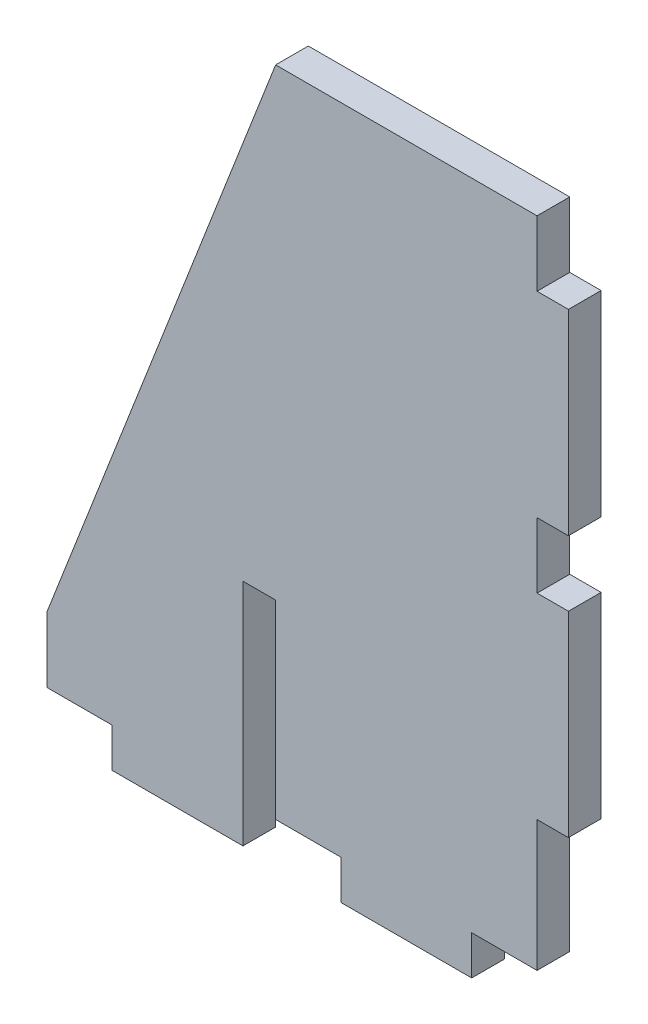
SolidWorks part; units mm, degrees
ref_plane "Front Plane" through (0, 0, 0) normal (0, 0, 1) x (1, 0, 0)
ref_plane "Top Plane" through (0, 0, 0) normal (0, 1, 0) x (1, 0, 0)
ref_plane "Right Plane" through (0, 0, 0) normal (1, 0, 0) x (0, 0, -1)
sketch "Sketch1" plane through (0, 0, 0) normal (0, 0, 1) x (1, 0, 0)
  line L1 (0, 0) -> (-6.35, 0)
  line L2 (0, 0) -> (0, 12.7)
  line L3 (0, 63.5) -> (-25.4, 63.5)
  line L6 (-28.575, 0) -> (-28.575, 18.4658)
  line L14 (-19.05, 0) -> (-19.05, -3.81)
  line L15 (-19.05, -3.81) -> (-6.35, -3.81)
  line L16 (-6.35, -3.81) -> (-6.35, 0)
  line L19 (-47.625, 0) -> (-47.625, 6.35)
  line L20 (-47.625, 6.35) -> (-25.4, 63.5)
  line L21 (0, 57.15) -> (3.048, 57.15)
  line L22 (3.048, 57.15) -> (3.048, 38.1)
  line L23 (3.048, 38.1) -> (0, 38.1)
  line L24 (0, 31.75) -> (3.048, 31.75)
  line L25 (3.048, 31.75) -> (3.048, 12.7)
  line L26 (3.048, 12.7) -> (0, 12.7)
  line L27 (0, 57.15) -> (0, 63.5)
  line L28 (0, 31.75) -> (0, 38.1)
  line L30 (-19.05, 0) -> (-25.4, 0)
  line L31 (-25.4, 0) -> (-25.4, 18.4658)
  line L32 (-25.4, 18.4658) -> (-28.575, 18.4658)
  line L33 (-28.575, 0) -> (-28.575, -3.81)
  line L34 (-28.575, -3.81) -> (-41.275, -3.81)
  line L35 (-41.275, -3.81) -> (-41.275, 0)
  line L36 (-41.275, 0) -> (-47.625, 0)
  dimension "D1" = 63.5
  dimension "D2" = 3.81
  dimension "D3" = 12.7
  dimension "D4" = 6.35
  dimension "D5" = 3.175
  dimension "D6" = 12.7
  dimension "D7" = 6.35
  dimension "D8" = 25.4
  dimension "D9" = 22.2758
  dimension "D10" = 3.048
  dimension "D11" = 6.35
  dimension "D12" = 6.35
  dimension "D13" = 3.048
  dimension "D14" = 19.05
  dimension "D15" = 19.05
  dimension "D16" = 12.7
  dimension "D17" = 38.1
extrude "Boss-Extrude1" add sketch "Sketch1" along normal blind 3.175 contours L14 L15 L16 L1 L2 L26 L25 L24 L28 L23 L22 L21 L27 L3 L20 L19 L36 L35 L34 L33 L6 L32 L31 L30
sketch "Sketch2" plane through (0, 0, 3.175) normal (0, 0, 1) x (1, 0, 0)
  line L32 (-25.4, 0) -> (-19.05, 0)
  line L33 (-19.05, 0) -> (-19.05, -3.81)
  line L34 (-19.05, -3.81) -> (-6.35, -3.81)
  line L35 (-6.35, -3.81) -> (-6.35, 0)
  line L36 (-6.35, 0) -> (0, 0)
  line L37 (0, 0) -> (0, 12.7)
  line L38 (0, 12.7) -> (3.048, 12.7)
  line L39 (3.048, 12.7) -> (3.048, 31.75)
  line L40 (3.048, 31.75) -> (0, 31.75)
  line L41 (0, 31.75) -> (0, 38.1)
  line L42 (0, 38.1) -> (3.048, 38.1)
  line L43 (3.048, 38.1) -> (3.048, 57.15)
  line L44 (3.048, 57.15) -> (0, 57.15)
  line L45 (0, 57.15) -> (0, 63.5)
  line L46 (0, 63.5) -> (-25.4, 63.5)
  line L47 (-25.4, 63.5) -> (-47.625, 6.35)
  line L48 (-47.625, 6.35) -> (-47.625, 0)
  line L49 (-25.4, 0) -> (-19.05, 0)
  line L54 (-28.575, -3.81) -> (-28.575, 18.4658)
  line L56 (-19.05, 0) -> (-19.05, -3.81)
  line L57 (-19.05, -3.81) -> (-6.35, -3.81)
  line L58 (-6.35, -3.81) -> (-6.35, 0)
  line L59 (-6.35, 0) -> (0, 0)
  line L60 (0, 0) -> (0, 12.7)
  line L61 (0, 12.7) -> (3.048, 12.7)
  line L62 (3.048, 12.7) -> (3.048, 31.75)
  line L63 (3.048, 31.75) -> (0, 31.75)
  line L64 (0, 31.75) -> (0, 38.1)
  line L65 (0, 38.1) -> (3.048, 38.1)
  line L66 (3.048, 38.1) -> (3.048, 57.15)
  line L67 (3.048, 57.15) -> (0, 57.15)
  line L68 (0, 57.15) -> (0, 63.5)
  line L69 (0, 63.5) -> (-25.4, 63.5)
  line L70 (-25.4, 63.5) -> (-47.625, 6.35)
  line L71 (-47.625, 6.35) -> (-47.625, 0)
  line L77 (-28.575, -3.81) -> (-28.575, 18.4658)
  line L88 (-47.625, 0) -> (-41.275, 0)
  line L89 (-47.625, 0) -> (-41.275, 0)
  line L90 (-41.275, 0) -> (-41.275, -3.81)
  line L91 (-41.275, 0) -> (-41.275, -3.81)
  line L92 (-41.275, -3.81) -> (-28.575, -3.81)
  line L93 (-41.275, -3.81) -> (-28.575, -3.81)
  line L94 (-28.575, 18.4658) -> (-25.4, 18.4658)
  line L95 (-28.575, 18.4658) -> (-25.4, 18.4658)
  line L96 (-25.4, 18.4658) -> (-25.4, 0)
  line L97 (-25.4, 18.4658) -> (-25.4, 0)
  dimension "D1" = 0
extrude "kerf" add sketch "Sketch2" against normal through all
